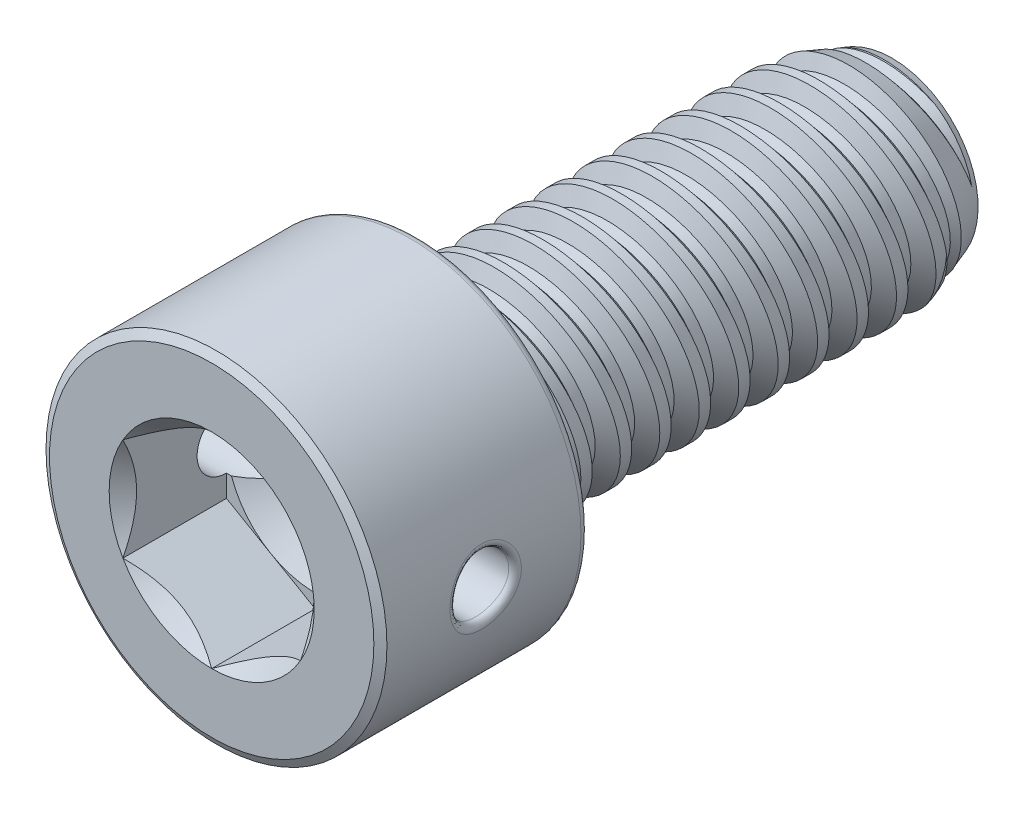
SolidWorks part; units mm, degrees
ref_plane "Front" through (0, 0, 0) normal (0, 0, 1) x (1, 0, 0)
ref_plane "Top" through (0, 0, 0) normal (0, 1, 0) x (1, 0, 0)
ref_plane "Right" through (0, 0, 0) normal (1, 0, 0) x (0, 0, -1)
sketch "Sketch1" plane through (0, 0, 0) normal (1, 0, 0) x (0, 0, -1)
  line L0 (0, 0) -> (-0.9525, 0) construction
  line L1 (0, 0) -> (9.525, 0)
  line L2 (0, 0) -> (0, 2.0828)
  line L3 (0, 2.0828) -> (9.525, 2.0828)
  line L4 (9.525, 0) -> (9.525, 2.0828)
  line L5 (0, -2.0828) -> (9.525, -2.0828) construction
  dimension "D1" = 0.9525
  dimension "Thread Dia" = 4.1656
  dimension "Screw Length" = 9.525
revolve "Revolve1" add sketch "Sketch1" angle 360 about L0
sketch "Sketch2" plane through (0, 0, 0) normal (1, 0, 0) x (0, 0, -1)
  line L0 (0, 2.0828) -> (0, -2.0828) construction
  line L1 (0, -2.0828) -> (0.7938, -2.0828) construction
  line L2 (0.7938, -2.0828) -> (0, 2.0828) construction
  line L3 (0, 2.0828) -> (0.0975, 2.1014) construction
  line L4 (0.0975, 2.1014) -> (0.7797, 2.2314)
  line L5 (0.7797, 2.2314) -> (0.6165, 1.7629)
  line L6 (0.6165, 1.7629) -> (0.4215, 1.7258)
  line L7 (0.4215, 1.7258) -> (0.0975, 2.1014)
  line L8 (0.519, 1.7443) -> (0.4386, 2.1664) construction
  line L9 (0, -2.0828) -> (9.525, -2.0828) construction
  line L10 (0, 2.0828) -> (9.525, 2.0828) construction
  line L12 (0.4545, 2.0828) -> (1.2483, -2.0828) construction
  line L13 (0, -0.1622) -> (1.7028, 0.1622) construction
  line L15 (0, 0) -> (0, 2.0828) construction
  point P19 (0.8514, 0)
  dimension "D1" = 60
  dimension "Thread Pitch" = 0.7937
  dimension "D2" = 0.0992
  dimension "D3" = 0.1984
  dimension "D4" = 0.7937
revolve "Cut-Revolve1" cut sketch "Sketch2" angle 360 about L13
sketch "Sketch3" plane through (0, 0, 0) normal (1, 0, 0) x (0, 0, -1)
  line L0 (9.525, 1.7258) -> (8.5441, 2.0828)
  line L1 (8.5441, 2.0828) -> (9.525, 2.0828)
  line L2 (9.525, 2.0828) -> (9.525, 1.7258)
  line L3 (0, 2.0828) -> (9.525, 2.0828) construction
  line L4 (9.525, 0) -> (9.525, 2.0828) construction
  line L5 (8.5441, 0) -> (0, 0) construction
  line L6 (8.5441, 2.0828) -> (8.5441, -2.0828) construction
  line L7 (0, -2.0828) -> (9.525, -2.0828) construction
  dimension "D1" = 20
  dimension "D2" = 4.1656
revolve "Cut-Revolve2" cut sketch "Sketch3" angle 360 about L5
pattern_linear "LPattern1" count 12 spacing 0.7937 along (0, 0, -1) of "Cut-Revolve1"
pattern_linear "LPattern2" count 2 spacing 0.7937 along (0, 0, 1) of "Cut-Revolve1"
sketch "Sketch4" plane through (0, 0, 0) normal (0, 0, 1) x (1, 0, 0)
  circle A0 centre (0, 0) radius 3.429
  dimension "Head Dia" = 6.858
extrude "Extrude1" add sketch "Sketch4" along normal blind 4.1656
sketch "Sketch9" plane through (0, 0, 0) normal (1, 0, 0) x (0, 0, -1)
  line L0 (0, 0) -> (-4.1656, 0) construction
  line L1 (-4.1656, 3.429) -> (-4.1656, -3.429) construction
  circle A0 centre (-2.0828, 0) radius 0.5905
  dimension "Hole Dia" = 1.1811
extrude "Cut-Extrude6" cut sketch "Sketch9" against normal through all and the other way through all
fillet "Fillet1" radius 0.1666 1 edges at (3.429, 0, 0)
chamfer "Chamfer1" distance 0.1666 angle 30 1 edges at (3.429, 0, 4.1656)
sketch "Sketch6" plane through (0, 0, 4.1656) normal (0, 0, 1) x (1, 0, 0)
  line L1 (0, -2.0622) -> (1.7859, -1.0311)
  line L2 (1.7859, -1.0311) -> (1.7859, 1.0311)
  line L3 (1.7859, 1.0311) -> (0, 2.0622)
  line L4 (0, 2.0622) -> (-1.7859, 1.0311)
  line L5 (-1.7859, 1.0311) -> (-1.7859, -1.0311)
  line L6 (-1.7859, -1.0311) -> (0, -2.0622)
  circle A0 centre (0, 0) radius 1.7859 construction
  dimension "Hex" = 3.5719
extrude "Cut-Extrude1" cut sketch "Sketch6" against normal blind 2.0828
sketch "Sketch7" plane through (0, 0, 4.1656) normal (0, 0, 1) x (1, 0, 0)
  circle A0 centre (0, 0) radius 2.0622
extrude "Cut-Extrude4" cut sketch "Sketch7" against normal blind 2.0828 draft 45
sketch "Sketch8" plane through (0, 0, 2.0828) normal (0, 0, 1) x (1, 0, 0)
  circle A0 centre (0, 0) radius 1.7859 construction
  circle A1 centre (0, 0) radius 1.7859
extrude "Cut-Extrude5" cut sketch "Sketch8" against normal blind 0.6943 draft 60
fillet "Fillet2" radius 0.127 2 edges at (-3.4267, 0.1261, 1.5059) (3.4267, 0.1261, 2.6597)
equation "\"D1@Sketch1\"=\"Screw Length@Sketch1\"/10"
equation "\"D2@Sketch2\"=\"Thread Pitch@Sketch2\"/8"
equation "\"D3@Sketch2\"=\"Thread Pitch@Sketch2\"/4"
equation "\"D4@Sketch2\"=\"Thread Pitch@Sketch2\""
equation "\"D3@LPattern1\"=\"Thread Pitch@Sketch2\""
equation "\"D1@Fillet1\"=\"Thread Dia@Sketch1\"/25"
equation "\"D1@Chamfer1\"=\"D1@Fillet1\""
equation "\"D1@Cut-Extrude1\"=\"Head Height@Extrude1\"/2"
equation "\"D1@Cut-Extrude4\"=\"D1@Cut-Extrude1\""
equation "\"D1@Cut-Extrude5\"=\"D1@Cut-Extrude1\"/3"
equation "\"D1@LPattern1\"=\"Screw Length@Sketch1\"/\"Thread Pitch@Sketch2\""
equation "\"D3@LPattern2\"=\"Thread Pitch@Sketch2\""
